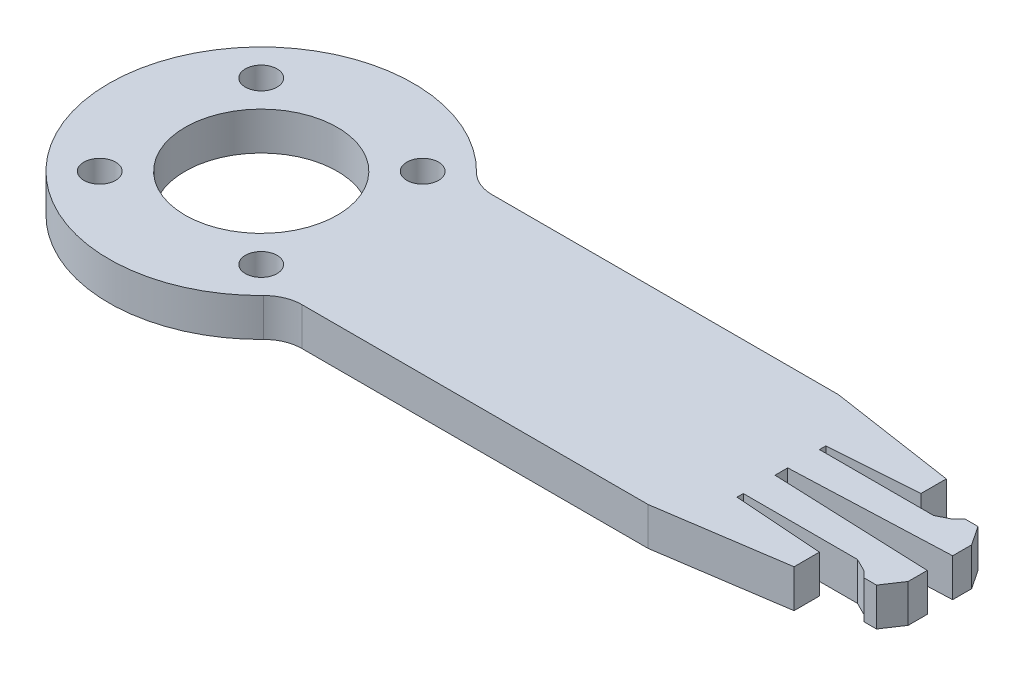
SolidWorks part; units mm, degrees
material "Lasercut ABS"
ref_plane "Front Plane" through (0, 0, 0) normal (0, 0, 1) x (1, 0, 0)
ref_plane "Top Plane" through (0, 0, 0) normal (0, 1, 0) x (1, 0, 0)
ref_plane "Right Plane" through (0, 0, 0) normal (1, 0, 0) x (0, 0, -1)
sketch "Sketch1" plane through (0, 0, 0) normal (0, 1, 0) x (1, 0, 0)
  line L1 (-6.364, 6.364) -> (6.364, -6.364) construction
  line L2 (-6.364, -6.364) -> (6.364, 6.364) construction
  line L4 (9.3675, 7.5) -> (38, 7.5)
  line L6 (9.3675, -7.5) -> (38, -7.5)
  circle A0 centre (0, 0) radius 6
  circle A1 centre (0, 0) radius 9 construction
  circle A2 centre (6.364, 6.364) radius 1.25
  circle A3 centre (-6.364, 6.364) radius 1.25
  circle A4 centre (-6.364, -6.364) radius 1.25
  circle A5 centre (6.364, -6.364) radius 1.25
  arc A6 (9.3675, 7.5) -> (9.3675, -7.5) centre (0, 0) ccw
  line B0 (38, 0) -> (41, 0) construction
  line B1 (41, 0.5) -> (41, -0.5)
  line B2 (41, 0.5) -> (53.5, 1)
  line B3 (53.5, 1) -> (53.5, 2.5)
  line B4 (53.5, 2.5) -> (52.5, 4)
  line B5 (52.5, 4) -> (51.5, 4)
  line B6 (51.5, 4) -> (51, 3.5)
  line B7 (51, 3.5) -> (50, 3)
  line B8 (50, 3) -> (41, 3)
  line B9 (41, 3) -> (41, 3.5)
  line B10 (41, 3.5) -> (48, 4)
  line B11 (48, 4) -> (48, 6)
  line B12 (48, 6) -> (38, 7.5)
  line B13 (41, -0.5) -> (53.5, -1)
  line B14 (53.5, -1) -> (53.5, -2.5)
  line B15 (53.5, -2.5) -> (52.5, -4)
  line B16 (52.5, -4) -> (51.5, -4)
  line B17 (51.5, -4) -> (51, -3.5)
  line B18 (51, -3.5) -> (50, -3)
  line B19 (50, -3) -> (41, -3)
  line B20 (41, -3) -> (41, -3.5)
  line B21 (41, -3.5) -> (48, -4)
  line B22 (48, -4) -> (48, -6)
  line B23 (48, -6) -> (38, -7.5)
  dimension "D1" = 12
  dimension "D5" = 18
  dimension "D6" = 2.5
  dimension "D7" = 24
  dimension "D2" = 45
  dimension "D3" = 48
sketch_block_instance "Block-Snap-Textile-1"
sketch_block "Block-Snap-Textile" parameters "D1"=3, "D2"=1, "D3"=2, "D4"=1.5, "D5"=10, "D6"=0.5, "D7"=9, "D8"=1, "D9"=0.5, "D10"=0.5, "D11"=0.5, "D12"=1, "D13"=12.5, "D14"=0.5, "D15"=0.5, "D16"=1.5, "D17"=1.5
extrude "Boss-Extrude1" add sketch "Sketch1" along normal mid plane 3
fillet "Fillet1" radius 3 2 edges at (9.3675, 0, 7.5) (9.3675, 0, -7.5)
sketch "Sketch2" plane through (0, 1.5, 0) normal (0, -1, 0) x (1, 0, 0)
  line L0 (28, -1) -> (12, -1) construction
  line L1 (28, 2.5) -> (12, 2.5) construction
  text T0 "M8" font "1CamBam_Stick_3" height 2.5
  text T1 "ONO V2" font "1CamBam_Stick_3" height 2.5
  dimension "D1" = 3.5
  dimension "D2" = 16
  dimension "D3" = 12
  dimension "D4" = 1
